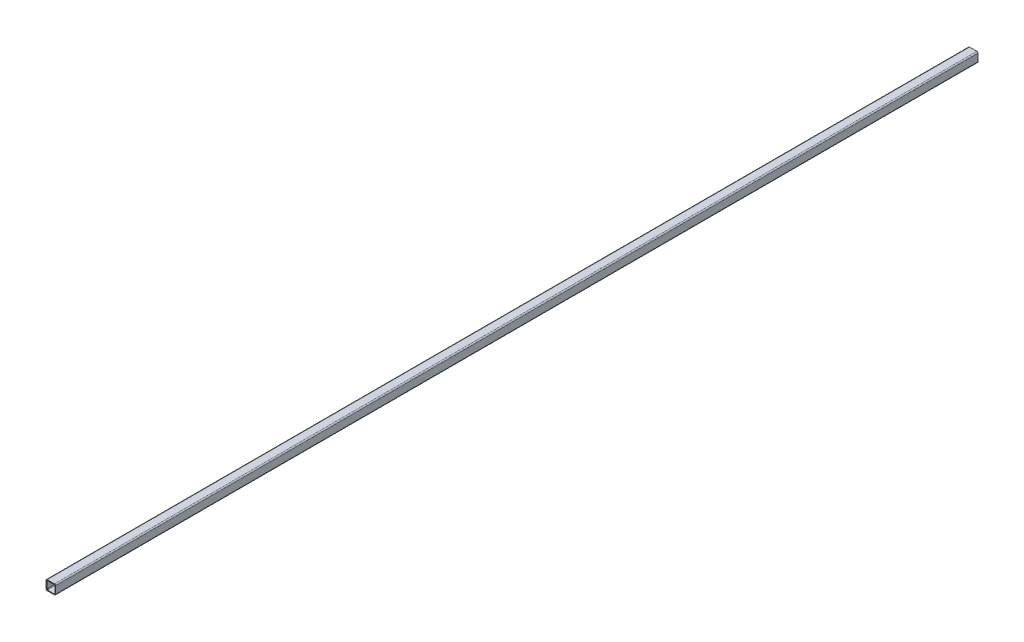
SolidWorks part; units mm, degrees
ref_plane "Front Plane" through (0, 0, 0) normal (0, 0, 1) x (1, 0, 0)
ref_plane "Top Plane" through (0, 0, 0) normal (0, 1, 0) x (1, 0, 0)
ref_plane "Right Plane" through (0, 0, 0) normal (1, 0, 0) x (0, 0, -1)
sketch "Sketch1" plane through (0, 0, 0) normal (0, 0, 1) x (1, 0, 0)
  line L0 (-10.668, -10.668) -> (-10.668, 10.668)
  line L1 (12.7, -12.7) -> (-12.7, -12.7)
  line L2 (12.7, -12.7) -> (12.7, 12.7)
  line L3 (12.7, 12.7) -> (-12.7, 12.7)
  line L4 (-12.7, -12.7) -> (-12.7, 12.7)
  line L5 (12.7, -12.7) -> (-12.7, 12.7) construction
  line L6 (12.7, 12.7) -> (-12.7, -12.7) construction
  line L7 (10.668, 10.668) -> (-10.668, 10.668)
  line L8 (10.668, -10.668) -> (10.668, 10.668)
  line L9 (10.668, -10.668) -> (-10.668, -10.668)
  point P0 (0, 0)
  dimension "Rail Width" = 25.4
  dimension "Rail Height" = 25.4
  dimension "Wall Thickness" = 2.032
sketch "Sketch2" plane through (0, 0, 0) normal (1, 0, 0) x (0, 0, -1)
  line L0 (-1219.2, 0) -> (1219.2, 0) construction
  line L1 (-1219.2, -12.7) -> (-1219.2, 12.7) construction
  line L2 (1219.2, -12.7) -> (1219.2, 12.7) construction
  point P0 (-1187.45, 0)
  point P3 (1187.45, 0)
  point P4 (0, 0)
  point P9 (-1219.2, 0)
  point P12 (1219.2, 0)
  dimension "D1" = 31.75
  dimension "D2" = 31.75
  dimension "D3" = 25.4
  dimension "Length" = 2438.4
sketch "Sketch3" plane through (0, 0, 0) normal (0, 0, 1) x (1, 0, 0)
  line L0 (10.668, -10.668) -> (-10.668, -10.668) construction
  line L1 (10.668, -10.668) -> (10.668, 10.668) construction
  line L2 (10.668, 10.668) -> (-10.668, 10.668) construction
  line L3 (-10.668, -10.668) -> (-10.668, 10.668) construction
  line L4 (12.7, -12.7) -> (-12.7, -12.7) construction
  line L5 (12.7, -12.7) -> (12.7, 12.7) construction
  line L6 (12.7, 12.7) -> (-12.7, 12.7) construction
  line L7 (-12.7, -12.7) -> (-12.7, 12.7) construction
  line L8 (10.668, -10.668) -> (-10.668, -10.668)
  line L9 (10.668, -10.668) -> (10.668, 10.668)
  line L10 (10.668, 10.668) -> (-10.668, 10.668)
  line L11 (-10.668, -10.668) -> (-10.668, 10.668)
  line L12 (12.7, -12.7) -> (-12.7, -12.7)
  line L13 (12.7, -12.7) -> (12.7, 12.7)
  line L14 (12.7, 12.7) -> (-12.7, 12.7)
  line L15 (-12.7, -12.7) -> (-12.7, 12.7)
extrude "Boss-Extrude1" add sketch "Sketch3" along normal up to vertex (1219.2 mm away) and the other way up to vertex (1219.2 mm away) up to point (0, 0, 1219.2) other way up to point (0, 0, -1219.2)
fillet "Fillet1" radius 3.175 4 edges at (-12.7, -12.7, 0) (12.7, -12.7, 0) (-12.7, 12.7, 0) (12.7, 12.7, 0)
fillet "Fillet2" radius 1.5875 4 edges at (10.668, -10.668, 0) (10.668, 10.668, 0) (-10.668, -10.668, 0) (-10.668, 10.668, 0)
equation "\"D1@Sketch2\"=\"Rail Width@Sketch1\"*1.25"
equation "\"D2@Sketch2\"=\"D1@Sketch2\""
equation "\"D3@Sketch2\"=\"Rail Height@Sketch1\""
equation "\"D1@Fillet1\"=\"Rail Width@Sketch1\"*.125"
equation "\"D1@Fillet2\"=\"Rail Width@Sketch1\"*.0625"
